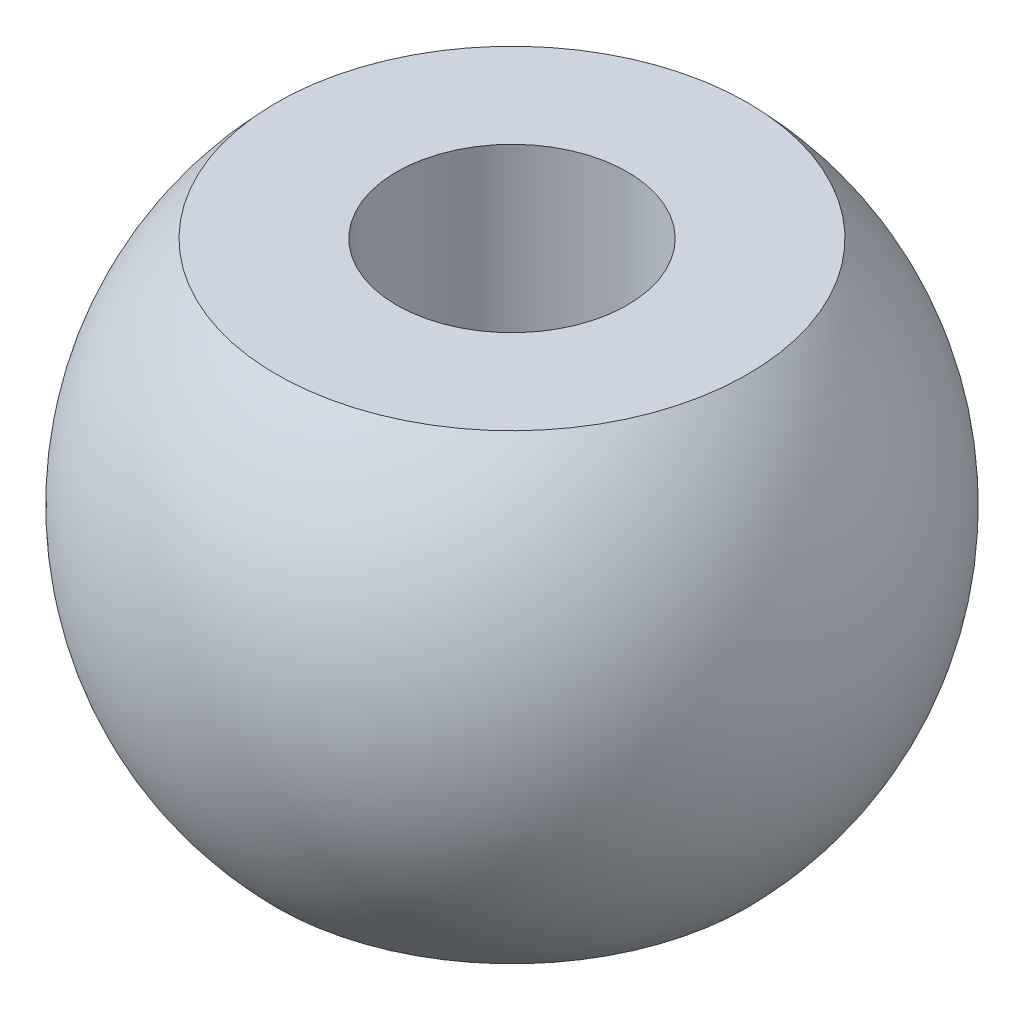
SolidWorks part; units mm, degrees
ref_plane "Front Plane" through (0, 0, 0) normal (0, 0, 1) x (1, 0, 0)
ref_plane "Top Plane" through (0, 0, 0) normal (0, 1, 0) x (1, 0, 0)
ref_plane "Right Plane" through (0, 0, 0) normal (1, 0, 0) x (0, 0, -1)
sketch "Sketch1" plane through (0, 0, 0) normal (0, 0, 1) x (1, 0, 0)
  line L0 (0, 0) -> (0, 20)
  arc A0 (0, 20) -> (0, 0) centre (0, 10) cw
  dimension "D1" = 20
revolve "Revolve1" add sketch "Sketch1" angle 360 about L0
sketch "Sketch3" plane through (0, 0, 0) normal (0, 0, 1) x (1, 0, 0)
  line L0 (0, 0) -> (0, 3) construction
  line L1 (0, 20) -> (0, 17) construction
  line L2 (0, 17) -> (-8.3098, 17)
  line L3 (-8.3098, 17) -> (-8.3098, 20)
  line L4 (-8.3098, 20) -> (9.4352, 20)
  line L5 (9.4352, 20) -> (9.4352, 17)
  line L6 (9.4352, 17) -> (0, 17)
  line L7 (0, 0) -> (9.4352, 0)
  line L8 (9.4352, 0) -> (9.4352, 3)
  line L9 (9.4352, 3) -> (-8.5787, 3)
  line L10 (-8.5787, 3) -> (-8.5787, 0)
  line L11 (-8.5787, 0) -> (0, 0)
  circle A0 centre (0, 10) radius 10 construction
  dimension "D1" = 3
  dimension "D2" = 3
extrude "Cut-Extrude1" cut sketch "Sketch3" against normal through all both and the other way through all
sketch "Sketch4" plane through (0, 17, 0) normal (0, 1, 0) x (1, 0, 0)
  circle A0 centre (0, 0) radius 3.5
  dimension "D1" = 7
extrude "Cut-Extrude2" cut sketch "Sketch4" against normal through all
